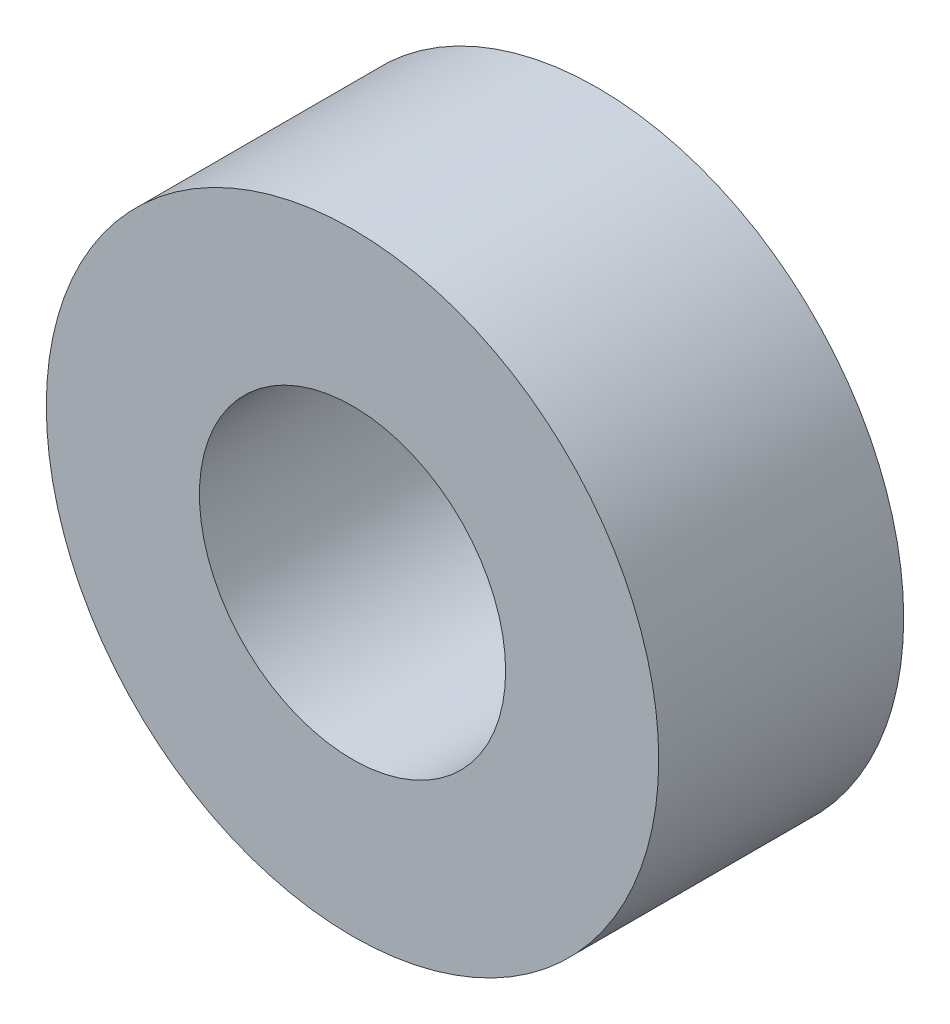
SolidWorks part; units mm, degrees
material "201 Annealed Stainless Steel (SS)"
ref_plane "Front Plane" through (0, 0, 0) normal (0, 0, 1) x (1, 0, 0)
ref_plane "Top Plane" through (0, 0, 0) normal (0, 1, 0) x (1, 0, 0)
ref_plane "Right Plane" through (0, 0, 0) normal (1, 0, 0) x (0, 0, -1)
sketch "Sketch1" plane through (0, 0, 0) normal (0, 0, 1) x (1, 0, 0)
  circle A0 centre (0, 0) radius 2.5
  circle A1 centre (0, 0) radius 5
  dimension "D1" = 10
  dimension "D2" = 5
extrude "Boss-Extrude1" add sketch "Sketch1" along normal blind 4
move or copy body "Body-Move/Copy1" [suppressed] bodies to move or copy 101 parameters "D1"=0, "D2"=0, "D3"=0
